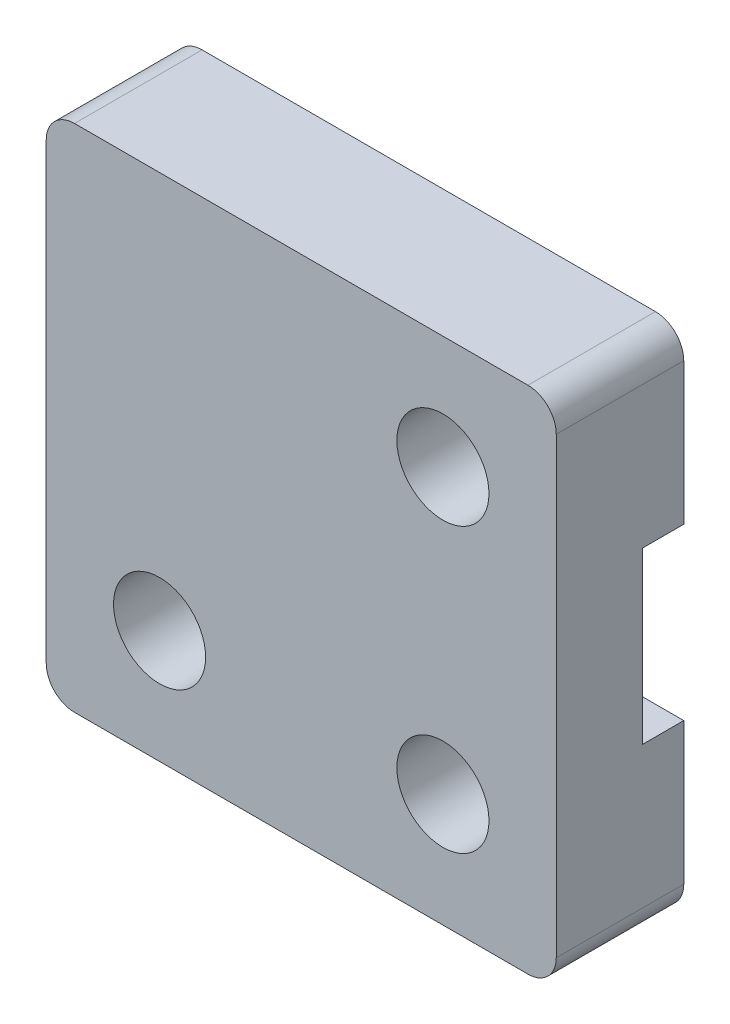
SolidWorks part; units mm, degrees
ref_plane "Front Plane" through (0, 0, 0) normal (0, 0, 1) x (1, 0, 0)
ref_plane "Top Plane" through (0, 0, 0) normal (0, 1, 0) x (1, 0, 0)
ref_plane "Right Plane" through (0, 0, 0) normal (1, 0, 0) x (0, 0, -1)
sketch "Sketch1" plane through (0, 0, 0) normal (0, 0, 1) x (1, 0, 0)
  line L0 (14, 14) -> (14, 4) construction
  line L1 (0, 0) -> (18, 0)
  line L2 (0, 0) -> (0, 18)
  line L3 (0, 18) -> (18, 18)
  line L4 (18, 0) -> (18, 18)
  line L5 (14, 4) -> (4, 4) construction
  circle A0 centre (4, 4) radius 1.625
  circle A1 centre (14, 4) radius 1.625
  circle A2 centre (14, 14) radius 1.625
  dimension "D1" = 3.25
  dimension "D2" = 18
  dimension "D3" = 10
  dimension "D4" = 4
  dimension "D5" = 4
extrude "Boss-Extrude1" add sketch "Sketch1" along normal blind 4
sketch "Sketch2" plane through (0, 0, 0) normal (0, 0, -1) x (-1, 0, 0)
  line L0 (-18, 0) -> (-18, 18) construction
  line L1 (-18, 12) -> (-17, 12)
  line L2 (-18, 12) -> (-18, 6)
  line L3 (-18, 6) -> (-17, 6)
  line L4 (-17, 12) -> (-17, 6)
  line L5 (-16, 12) -> (-16, 6)
  line L6 (-17, 12) -> (-16, 12)
  line L7 (-17, 12) -> (-17, 6)
  line L8 (-17, 6) -> (-16, 6)
  line L9 (-15, 12) -> (-15, 6)
  line L10 (-16, 12) -> (-15, 12)
  line L11 (-16, 12) -> (-16, 6)
  line L12 (-16, 6) -> (-15, 6)
  line L13 (-14, 12) -> (-14, 6)
  line L14 (-15, 12) -> (-14, 12)
  line L15 (-15, 12) -> (-15, 6)
  line L16 (-15, 6) -> (-14, 6)
  line L17 (-13, 12) -> (-13, 6)
  line L18 (-14, 12) -> (-13, 12)
  line L19 (-14, 12) -> (-14, 6)
  line L20 (-14, 6) -> (-13, 6)
  line L21 (-12, 12) -> (-12, 6)
  line L22 (-13, 12) -> (-12, 12)
  line L23 (-13, 12) -> (-13, 6)
  line L24 (-13, 6) -> (-12, 6)
  line L25 (-11, 12) -> (-11, 6)
  line L26 (-12, 12) -> (-11, 12)
  line L27 (-12, 12) -> (-12, 6)
  line L28 (-12, 6) -> (-11, 6)
  line L29 (-10, 12) -> (-10, 6)
  line L30 (-11, 12) -> (-10, 12)
  line L31 (-11, 12) -> (-11, 6)
  line L32 (-11, 6) -> (-10, 6)
  line L33 (-9, 12) -> (-9, 6)
  line L34 (-10, 12) -> (-9, 12)
  line L35 (-10, 12) -> (-10, 6)
  line L36 (-10, 6) -> (-9, 6)
  line L37 (-8, 12) -> (-8, 6)
  line L38 (-9, 12) -> (-8, 12)
  line L39 (-9, 12) -> (-9, 6)
  line L40 (-9, 6) -> (-8, 6)
  line L41 (-7, 12) -> (-7, 6)
  line L42 (-8, 12) -> (-7, 12)
  line L43 (-8, 12) -> (-8, 6)
  line L44 (-8, 6) -> (-7, 6)
  line L45 (-6, 12) -> (-6, 6)
  line L46 (-7, 12) -> (-6, 12)
  line L47 (-7, 12) -> (-7, 6)
  line L48 (-7, 6) -> (-6, 6)
  line L49 (-5, 12) -> (-5, 6)
  line L50 (-6, 12) -> (-5, 12)
  line L51 (-6, 12) -> (-6, 6)
  line L52 (-6, 6) -> (-5, 6)
  line L53 (-4, 12) -> (-4, 6)
  line L54 (-5, 12) -> (-4, 12)
  line L55 (-5, 12) -> (-5, 6)
  line L56 (-5, 6) -> (-4, 6)
  line L57 (-3, 12) -> (-3, 6)
  line L58 (-4, 12) -> (-3, 12)
  line L59 (-4, 12) -> (-4, 6)
  line L60 (-4, 6) -> (-3, 6)
  line L61 (-2, 12) -> (-2, 6)
  line L62 (-3, 12) -> (-2, 12)
  line L63 (-3, 12) -> (-3, 6)
  line L64 (-3, 6) -> (-2, 6)
  line L65 (-1, 12) -> (-1, 6)
  line L66 (-2, 12) -> (-1, 12)
  line L67 (-2, 12) -> (-2, 6)
  line L68 (-2, 6) -> (-1, 6)
  line L69 (0, 12) -> (0, 6)
  line L70 (-1, 12) -> (0, 12)
  line L71 (-1, 12) -> (-1, 6)
  line L72 (-1, 6) -> (0, 6)
  line M7 (-18, 18) -> (-18, 0)
  dimension "D1" = 6
  dimension "D2" = 1
  dimension "D3" = 6
  dimension "D4" = 18
extrude "Cut-Extrude1" cut sketch "Sketch2" against normal blind 0.95 contours L4 L1 L3 M7 | L5 L12 L9 L10 | L13 L20 L17 L18 | L21 L28 L25 L26 | L29 L36 L33 L34 | L37 L44 L41 L42 | L45 L52 L49 L50 | L53 L60 L57 L58 | L61 L68 L65 L66
sketch "Sketch3" plane through (0, 0, 0) normal (0, 0, -1) x (-1, 0, 0)
  line L0 (0, 18) -> (0, 0) construction
  line L1 (-18, 18) -> (0, 18)
  line L2 (-18, 18) -> (-18, 12)
  line L3 (-18, 12) -> (0, 12)
  line L4 (-2, 12) -> (-2, 6)
  line L5 (-1, 12) -> (-2, 12)
  line L6 (-1, 6) -> (-1, 12)
  line L7 (-2, 6) -> (-1, 6)
  line L8 (-2, 12) -> (-2, 6)
  line L9 (-1, 12) -> (-2, 12)
  line L10 (-1, 6) -> (-1, 12)
  line L11 (-2, 6) -> (-1, 6)
  line L12 (-4, 12) -> (-4, 6)
  line L13 (-3, 12) -> (-4, 12)
  line L14 (-3, 6) -> (-3, 12)
  line L15 (-4, 6) -> (-3, 6)
  line L16 (-4, 12) -> (-4, 6)
  line L17 (-3, 12) -> (-4, 12)
  line L18 (-3, 6) -> (-3, 12)
  line L19 (-4, 6) -> (-3, 6)
  line L20 (-6, 12) -> (-6, 6)
  line L21 (-5, 12) -> (-6, 12)
  line L22 (-5, 6) -> (-5, 12)
  line L23 (-6, 6) -> (-5, 6)
  line L24 (-6, 12) -> (-6, 6)
  line L25 (-5, 12) -> (-6, 12)
  line L26 (-5, 6) -> (-5, 12)
  line L27 (-6, 6) -> (-5, 6)
  line L28 (-8, 12) -> (-8, 6)
  line L29 (-7, 12) -> (-8, 12)
  line L30 (-7, 6) -> (-7, 12)
  line L31 (-8, 6) -> (-7, 6)
  line L32 (-8, 12) -> (-8, 6)
  line L33 (-7, 12) -> (-8, 12)
  line L34 (-7, 6) -> (-7, 12)
  line L35 (-8, 6) -> (-7, 6)
  line L36 (-10, 12) -> (-10, 6)
  line L37 (-9, 12) -> (-10, 12)
  line L38 (-9, 6) -> (-9, 12)
  line L39 (-10, 6) -> (-9, 6)
  line L40 (-10, 12) -> (-10, 6)
  line L41 (-9, 12) -> (-10, 12)
  line L42 (-9, 6) -> (-9, 12)
  line L43 (-10, 6) -> (-9, 6)
  line L44 (-12, 12) -> (-12, 6)
  line L45 (-11, 12) -> (-12, 12)
  line L46 (-11, 6) -> (-11, 12)
  line L47 (-12, 6) -> (-11, 6)
  line L48 (-12, 12) -> (-12, 6)
  line L49 (-11, 12) -> (-12, 12)
  line L50 (-11, 6) -> (-11, 12)
  line L51 (-12, 6) -> (-11, 6)
  line L52 (-14, 12) -> (-14, 6)
  line L53 (-13, 12) -> (-14, 12)
  line L54 (-13, 6) -> (-13, 12)
  line L55 (-14, 6) -> (-13, 6)
  line L56 (-14, 12) -> (-14, 6)
  line L57 (-13, 12) -> (-14, 12)
  line L58 (-13, 6) -> (-13, 12)
  line L59 (-14, 6) -> (-13, 6)
  line L60 (-16, 12) -> (-16, 6)
  line L61 (-15, 12) -> (-16, 12)
  line L62 (-15, 6) -> (-15, 12)
  line L63 (-16, 6) -> (-15, 6)
  line L64 (-16, 12) -> (-16, 6)
  line L65 (-15, 12) -> (-16, 12)
  line L66 (-15, 6) -> (-15, 12)
  line L67 (-16, 6) -> (-15, 6)
  line L68 (0, 18) -> (0, 12)
  line L70 (-18, 6) -> (0, 6)
  line L71 (-18, 6) -> (-18, 0)
  line L72 (-18, 0) -> (0, 0)
  line L73 (0, 6) -> (0, 0)
  circle A1 centre (-4, 4) radius 1.625
  circle A2 centre (-4, 4) radius 1.625
  circle A3 centre (-14, 4) radius 1.625
  circle A4 centre (-14, 4) radius 1.625
  circle A5 centre (-14, 14) radius 1.625
  circle A6 centre (-14, 14) radius 1.625
  line M36 (-17, 6) -> (-18, 6)
  line M37 (-18, 6) -> (-18, 0)
  line M38 (-18, 0) -> (0, 0)
  line M39 (0, 0) -> (0, 18)
  line M40 (0, 18) -> (-18, 18)
  line M41 (-18, 18) -> (-18, 12)
  line M42 (-18, 12) -> (-17, 12)
  line M45 (-16, 12) -> (-15, 12)
  line M47 (-15, 6) -> (-16, 6)
  line M49 (-14, 12) -> (-13, 12)
  line M51 (-13, 6) -> (-14, 6)
  line M53 (-12, 12) -> (-11, 12)
  line M55 (-11, 6) -> (-12, 6)
  line M57 (-10, 12) -> (-9, 12)
  line M59 (-9, 6) -> (-10, 6)
  line M61 (-8, 12) -> (-7, 12)
  line M63 (-7, 6) -> (-8, 6)
  line M65 (-6, 12) -> (-5, 12)
  line M67 (-5, 6) -> (-6, 6)
  line M69 (-4, 12) -> (-3, 12)
  line M71 (-3, 6) -> (-4, 6)
  line M73 (-2, 12) -> (-1, 12)
  line M75 (-1, 6) -> (-2, 6)
  circle M76 centre (-14, 4) radius 1.625
  circle M77 centre (-4, 4) radius 1.625
  circle M78 centre (-14, 14) radius 1.625
  dimension "D1" = 0
  dimension "D2" = 0
  dimension "D3" = 0
  dimension "D4" = 0
  dimension "D5" = 0
  dimension "D6" = 0
  dimension "D7" = 0
  dimension "D8" = 0
  dimension "D9" = 0
  dimension "D10" = 0
  dimension "D11" = 0
extrude "Boss-Extrude2" add sketch "Sketch3" along normal blind 0.5 contours L70 M36 M37 M38 M39 M75 M71 M67 M63 M59 M55 M51 M47 M76 M77 | L3 M42 M45 M49 M53 M57 M61 M65 M69 M73 M39 M40 M41 M78
fillet "Fillet1" radius 1 4 edges at (0, 0, 1.75) (18, 0, 1.75) (18, 18, 1.75) (0, 18, 1.75)
